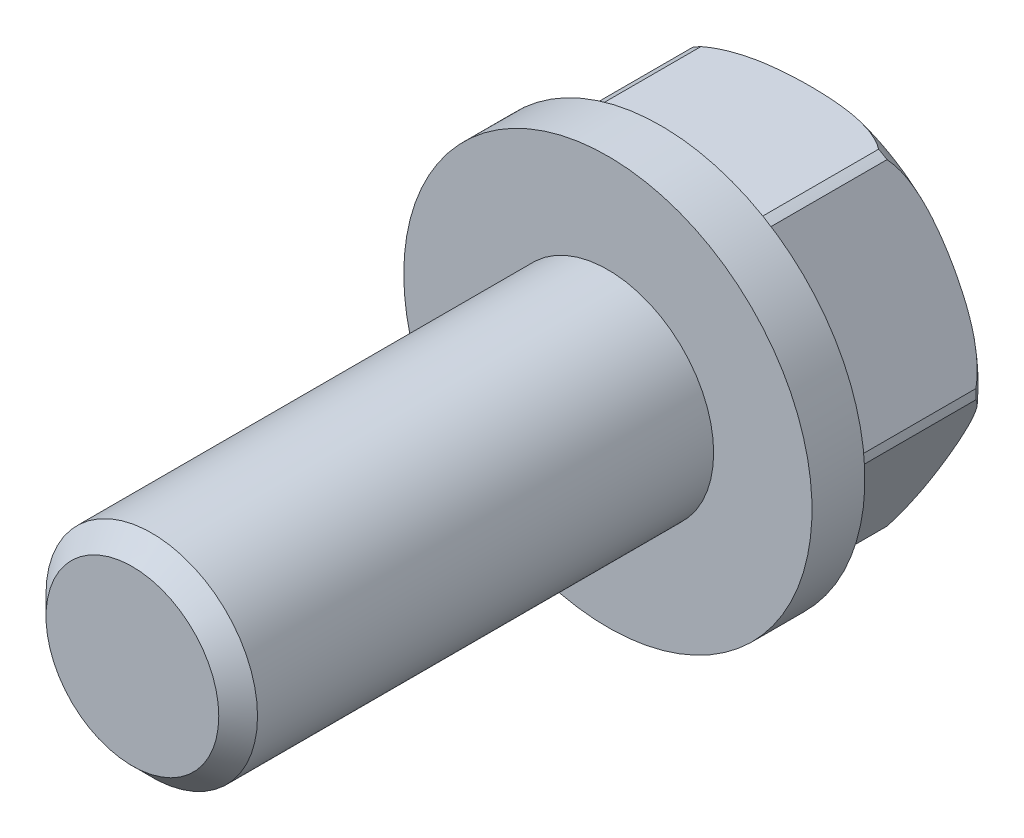
SolidWorks part; units mm, degrees
ref_plane "Front Plane" through (0, 0, 0) normal (0, 0, 1) x (1, 0, 0)
ref_plane "Top Plane" through (0, 0, 0) normal (0, 1, 0) x (1, 0, 0)
ref_plane "Right Plane" through (0, 0, 0) normal (1, 0, 0) x (0, 0, -1)
sketch "Sketch1" plane through (0, 0, 0) normal (0, 1, 0) x (1, 0, 0)
  line L0 (0, 24.8925) -> (0, -28.3259) construction
  line L1 (0, 14.7829) -> (0, -26.2127)
  line L2 (0, -26.2127) -> (-6.35, -26.2127)
  line L3 (-6.35, -26.2127) -> (-6.35, 2.3369)
  line L4 (-6.35, 2.3369) -> (-12.2555, 2.3369)
  line L5 (-12.2555, 2.3369) -> (-12.2555, 5.5119)
  line L7 (-12.2555, 5.5119) -> (-11.176, 5.5119)
  line L8 (-11.176, 5.5119) -> (-11.176, 14.7829)
  line L9 (-11.176, 14.7829) -> (0, 14.7829)
  point P3 (0, 0)
  point P5 (0, 14.2107)
  dimension "D1" = 24.511
  dimension "D2" = 40.9956
  dimension "D3" = 3.175
  dimension "D4" = 12.7
  dimension "D5" = 22.352
  dimension "D6" = 9.271
revolve "Revolve2" add sketch "Sketch1" angle 360 about L0
sketch "Sketch3" plane through (0, 0, -14.7829) normal (0, 0, -1) x (-1, 0, 0)
  line L0 (-5.334, 9.821) -> (5.334, 9.821)
  line L1 (5.8382, 9.5299) -> (11.1722, 0.2911)
  line L2 (11.1722, -0.2911) -> (5.8382, -9.5299)
  line L3 (5.334, -9.821) -> (-5.334, -9.821)
  line L4 (-5.8382, -9.5299) -> (-11.1722, -0.2911)
  line L5 (-11.1722, 0.2911) -> (-5.8382, 9.5299)
  circle A0 centre (0, 0) radius 11.176 construction
  circle A1 centre (0, 0) radius 11.176
  circle A2 centre (0, 0) radius 11.176
  circle A3 centre (0, 0) radius 11.176
  circle A4 centre (0, 0) radius 11.176
  circle A5 centre (0, 0) radius 11.176
  circle A6 centre (0, 0) radius 11.176
  circle M2 centre (0, 0) radius 11.176
  dimension "D1" = 10.668
  dimension "D2" = 6
extrude "Cut-Extrude1" cut sketch "Sketch3" against normal up to surface (9.271 mm away) contours L0 M2 | L5 M2 | L4 M2 | L3 M2 | L2 M2 | L1 M2 up to face at (-12.2555, 0, -5.5119)
sketch "Sketch4" plane through (0, 0, 0) normal (0, 1, 0) x (1, 0, 0)
  line L0 (8.6995, 14.7829) -> (11.176, 14.7829)
  line L1 (11.1722, 14.7829) -> (5.8382, 14.7829) construction
  line L2 (11.176, 14.7829) -> (11.176, 13.2589)
  line L3 (0, 20.1865) -> (0, 7.5242) construction
  arc A1 (11.176, 13.2589) -> (8.6995, 14.7829) centre (8.4347, 11.5785) ccw
  dimension "D1" = 22.352
  dimension "D2" = 17.399
  dimension "D3" = 1.524
revolve "Cut-Revolve1" cut sketch "Sketch4" angle 360 about L3
chamfer "Chamfer1" distance 1.1633 angle 45 1 edges at (-6.35, 0, 26.2127)
